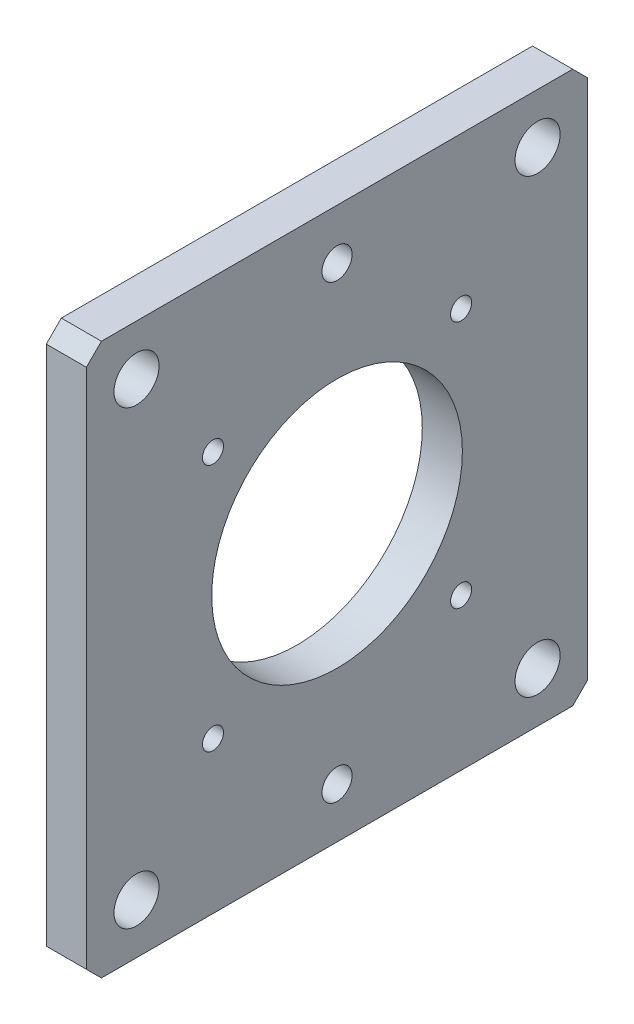
SolidWorks part; units mm, degrees
ref_plane "Front" through (0, 0, 0) normal (0, 0, 1) x (1, 0, 0)
ref_plane "Top" through (0, 0, 0) normal (0, 1, 0) x (1, 0, 0)
ref_plane "Right" through (0, 0, 0) normal (1, 0, 0) x (0, 0, -1)
sketch "Sketch2" plane through (0, 0, 0) normal (1, 0, 0) x (0, 0, -1)
  line L0 (0, 117.8398) -> (0, -6.6489) construction
  line L2 (50, 0) -> (-50, 0)
  line L3 (50, 0) -> (50, 110)
  line L4 (50, 110) -> (-50, 110)
  line L5 (-50, 0) -> (-50, 110)
  dimension "D1" = 100
  dimension "D2" = 110
extrude "Boss-Extrude1" add sketch "Sketch2" against normal blind 8
sketch "Sketch3" plane through (0, 0, 0) normal (1, 0, 0) x (0, 0, -1)
  line L0 (0, -4.848) -> (0, 117.2808) construction
  circle A0 centre (0, 55) radius 25
  dimension "D1" = 50
  dimension "D2" = 55
extrude "Cut-Extrude1" cut sketch "Sketch3" against normal through all
sketch "Sketch8" plane through (-8, 0, 0) normal (-1, 0, 0) x (0, 0, 1)
  circle A0 centre (0, 10) radius 3
  circle A1 centre (0, 100) radius 3
  dimension "D1" = 6
  dimension "D2" = 10
  dimension "D3" = 90
extrude "Cut-Extrude2" cut sketch "Sketch8" against normal through all
hole_wizard "Ø9.0 (9) Diameter Hole1" positions "Sketch5" profile "Sketch6" hole size "Ø9.0" standard "JIS" end condition through all
sketch "Sketch5" plane through (0, 0, 0) normal (1, 0, 0) x (0, 0, -1)
  line L0 (0, -6.0595) -> (0, 116.5914) construction
  line L2 (-50, 0) -> (50, 0) construction
  point P0 (-40, 100)
  point P6 (-40, 10)
  point P18 (40, 10)
  point P19 (40, 100)
  dimension "D1" = 80
  dimension "D2" = 10
  dimension "D3" = 90
sketch "Sketch6" plane through (0, 100, 40) normal (0, 1, 0) x (0, 0, -1)
  line L0 (0, 0) -> (0, 8)
  line L1 (0, 8) -> (4.5, 8)
  line L2 (4.5, 8) -> (4.5, 0)
  line L5 (4.5, 0) -> (0, 0)
  line L11 (0, -6.35) -> (0, 107.95) construction
  dimension "Thru Hole Dia." = 9
  dimension "Thru Hole Depth" = 8
hole_wizard "M5x0.8 Tapped Hole1" positions "Sketch10" profile "Sketch9" tap size "M5x0.8" standard "JIS" end condition through all
sketch "Sketch10" plane through (0, 0, 0) normal (1, 0, 0) x (0, 0, -1)
  line L5 (0, 55) -> (0, 90) construction
  line L7 (0, 55) -> (27.7674, 82.7674) construction
  circle A0 centre (0, 55) radius 35 construction
  circle A1 centre (0, 55) radius 25 construction
  point P0 (24.7487, 79.7487)
  point P20 (-24.7487, 79.7487)
  point P23 (-24.7487, 30.2513)
  point P26 (24.7487, 30.2513)
  dimension "D1" = 70
  dimension "D2" = 45
sketch "Sketch9" plane through (0, 79.7487, -24.7487) normal (0, 1, 0) x (0, 0, -1)
  line L0 (0, 0) -> (0, 8)
  line L1 (0, 8) -> (2.1, 8)
  line L2 (2.1, 8) -> (2.1, 0)
  line L5 (2.1, 0) -> (0, 0)
  line L11 (0, -6.35) -> (0, 107.95) construction
  dimension "Thru Tap Drill Dia." = 4.2
  dimension "Thru Tap Drill Depth" = 8
cosmetic thread "Hole Thread1" parameters "D2"=5
cosmetic thread "Hole Thread2" parameters "D2"=5
cosmetic thread "Hole Thread3" parameters "D2"=5
cosmetic thread "Hole Thread4" parameters "D2"=5
chamfer "Chamfer1" distance 3 angle 45 4 edges at (-4, 110, -50) (-4, 0, -50) (-4, 0, 50) (-4, 110, 50)
